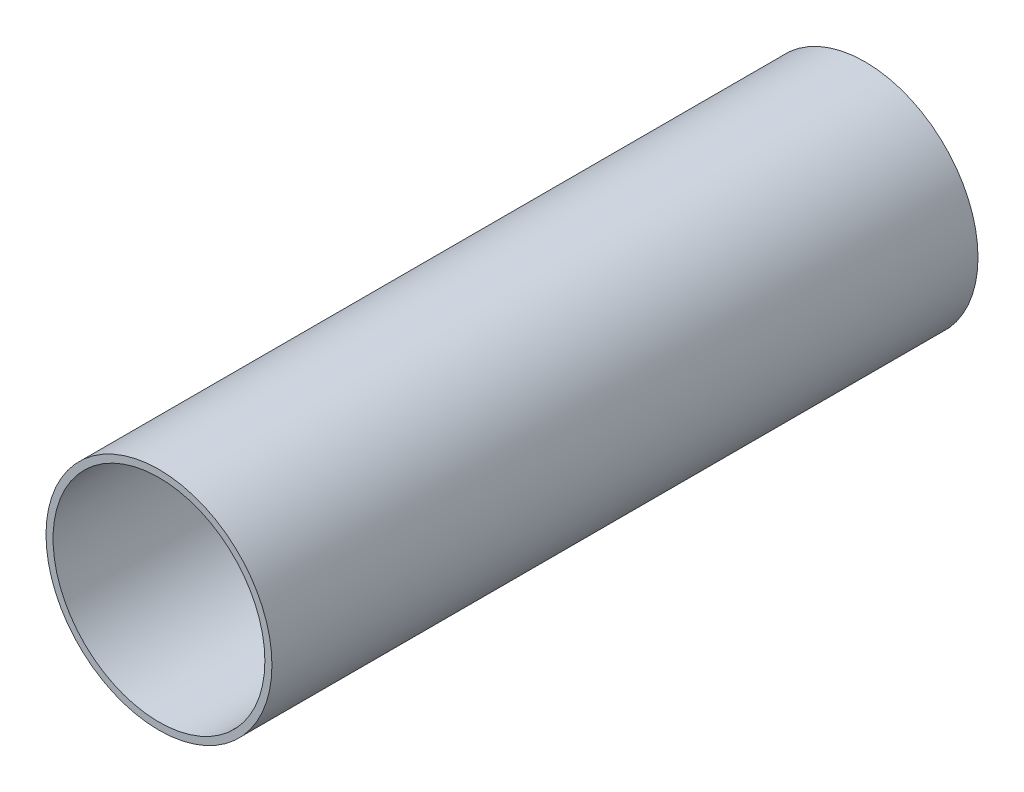
SolidWorks part; units mm, degrees
ref_plane "Front Plane" through (0, 0, 0) normal (0, 0, 1) x (1, 0, 0)
ref_plane "Top Plane" through (0, 0, 0) normal (0, 1, 0) x (1, 0, 0)
ref_plane "Right Plane" through (0, 0, 0) normal (1, 0, 0) x (0, 0, -1)
sketch "Sketch1" plane through (0, 0, 0) normal (0, 0, 1) x (1, 0, 0)
  circle A0 centre (0, 0) radius 32
  circle A1 centre (0, 0) radius 30
  dimension "D1" = 2
  dimension "D2" = 64
extrude "Boss-Extrude1" add sketch "Sketch1" along normal blind 200
